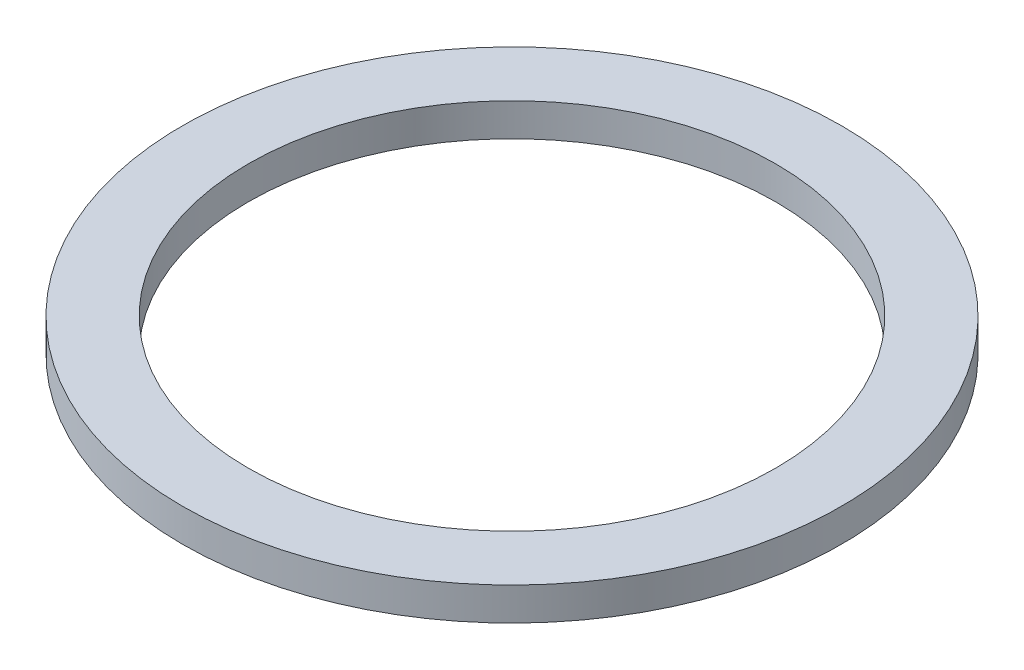
SolidWorks part; units mm, degrees
ref_plane "前视基准面" through (0, 0, 0) normal (0, 0, 1) x (1, 0, 0)
ref_plane "上视基准面" through (0, 0, 0) normal (0, 1, 0) x (1, 0, 0)
ref_plane "右视基准面" through (0, 0, 0) normal (1, 0, 0) x (0, 0, -1)
sketch "草图1" plane through (0, 0, 0) normal (0, 1, 0) x (1, 0, 0)
  circle A0 centre (0, 0) radius 1
extrude "拉伸-薄壁1" add sketch "草图1" along normal blind 0.1 thin thin type one direction reverse wall 0.2
sketch "草图2" plane through (0, 0.1, 0) normal (0, 1, 0) x (1, 0, 0)
  point P0 (0, 0)
